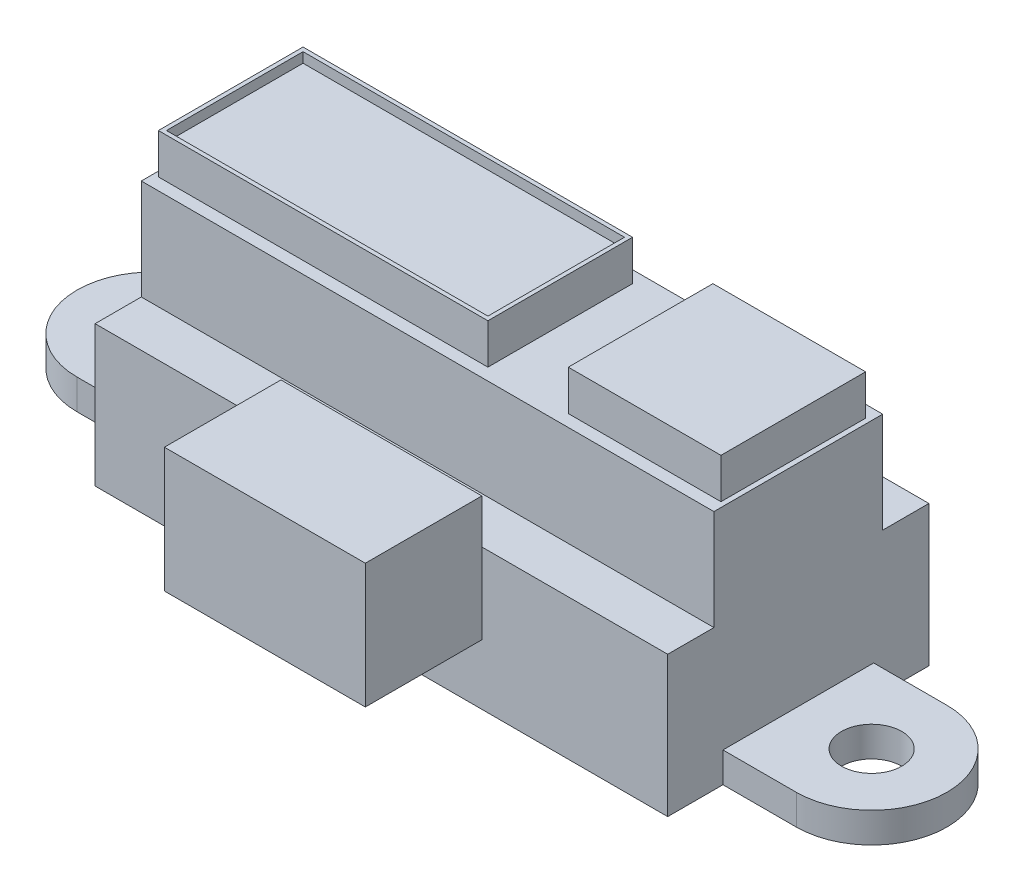
SolidWorks part; units mm, degrees
ref_plane "Front" through (0, 0, 0) normal (0, 0, 1) x (1, 0, 0)
ref_plane "Top" through (0, 0, 0) normal (0, 1, 0) x (1, 0, 0)
ref_plane "Right" through (0, 0, 0) normal (1, 0, 0) x (0, 0, -1)
sketch "Sketch1" plane through (0, 0, 0) normal (0, 1, 0) x (1, 0, 0)
  line L1 (-14.25, -6.5) -> (14.25, -6.5)
  line L2 (-14.25, -6.5) -> (-14.25, 6.5)
  line L3 (-14.25, 6.5) -> (14.25, 6.5)
  line L4 (14.25, -6.5) -> (14.25, 6.5)
  line L5 (-14.25, -6.5) -> (14.25, 6.5) construction
  line L6 (-14.25, 6.5) -> (14.25, -6.5) construction
  point P0 (0, 0)
  dimension "D1" = 28.5
  dimension "D2" = 13
extrude "Boss-Extrude1" add sketch "Sketch1" along normal blind 7
sketch "Sketch2" plane through (0, 7, 0) normal (0, 1, 0) x (1, 0, 0)
  line L0 (14.25, -6.5) -> (14.25, 6.5) construction
  line L1 (-14.25, -4.2) -> (14.25, -4.2)
  line L2 (-14.25, -4.2) -> (-14.25, 4.2)
  line L3 (-14.25, 4.2) -> (14.25, 4.2)
  line L4 (14.25, -4.2) -> (14.25, 4.2)
  line L5 (-14.25, -4.2) -> (14.25, 4.2) construction
  line L6 (-14.25, 4.2) -> (14.25, -4.2) construction
  point P0 (0, 0)
  dimension "D1" = 8.4
extrude "Boss-Extrude2" add sketch "Sketch2" along normal blind 5
sketch "Sketch3" plane through (0, 12, 0) normal (0, 1, 0) x (1, 0, 0)
  line L1 (-14, -3.6) -> (14, -3.6) construction
  line L2 (-14, -3.6) -> (-14, 3.6) construction
  line L3 (-14, 3.6) -> (14, 3.6) construction
  line L4 (14, -3.6) -> (14, 3.6) construction
  line L5 (-14, -3.6) -> (14, 3.6) construction
  line L6 (-14, 3.6) -> (14, -3.6) construction
  point P0 (0, 0)
  point P6 (0, 0)
  point P7 (0, 0)
  dimension "D1" = 28
  dimension "D2" = 7.2
sketch "Sketch4" plane through (0, 12, 0) normal (0, 1, 0) x (1, 0, 0)
  line L1 (-14, 3.6) -> (2.4, 3.6)
  line L2 (-14, 3.6) -> (-14, -3.6)
  line L3 (-14, -3.6) -> (2.4, -3.6)
  line L4 (2.4, 3.6) -> (2.4, -3.6)
  line L5 (14, 3.6) -> (6.4, 3.6)
  line L6 (14, 3.6) -> (14, -3.6)
  line L7 (14, -3.6) -> (6.4, -3.6)
  line L8 (6.4, 3.6) -> (6.4, -3.6)
  point P5 (6.4, -1.4365)
  point P14 (0, 0)
  dimension "D1" = 16.4
  dimension "D2" = 7.6
extrude "Boss-Extrude3" add sketch "Sketch4" along normal blind 2
sketch "Sketch5" plane through (0, 14, 0) normal (0, 1, 0) x (1, 0, 0)
  line L9 (-13.8, 3.4) -> (-13.8, -3.4)
  line L10 (-13.8, -3.4) -> (2.2, -3.4)
  line L11 (2.2, -3.4) -> (2.2, 3.4)
  line L12 (2.2, 3.4) -> (-13.8, 3.4)
  line L13 (-13.8, 3.4) -> (-13.8, -3.4)
  line L14 (-13.8, -3.4) -> (2.2, -3.4)
  line L15 (2.2, -3.4) -> (2.2, 3.4)
  line L16 (2.2, 3.4) -> (-13.8, 3.4)
  dimension "D1" = 0.2
extrude "Cut-Extrude1" cut sketch "Sketch5" against normal blind 0.5
sketch "Sketch6" plane through (0, 0, 0) normal (0, 1, 0) x (1, 0, 0)
  line L0 (-14.25, 6.5) -> (-14.25, -6.5) construction
  line L1 (-14.25, 6.5) -> (-14.25, -6.5) construction
  line L2 (14.25, 0) -> (-14.25, 0) construction
  line L6 (-14.25, 3.75) -> (-14.25, -3.75)
  line L7 (-17.9, 3.75) -> (-17.9, 0) construction
  line L8 (-17.9, 0) -> (-17.9, -3.75) construction
  line L9 (-14.25, -3.75) -> (-17.9, -3.75)
  line L10 (-14.25, 3.75) -> (-17.9, 3.75)
  arc A0 (-17.9, 3.75) -> (-17.9, -3.75) centre (-17.9, 0) ccw
  circle A1 centre (-17.9, 0) radius 1.5
  point P9 (0, 0)
  point P14 (-21.65, 0)
  point P18 (-21.65, 0)
  dimension "D1" = 3.75
  dimension "D3" = 3
  dimension "D2" = 7.4
extrude "Boss-Extrude4" add sketch "Sketch6" along normal blind 1.5
mirror "Mirror1" about plane through (0, 0, 0) normal (1, 0, 0) of "Boss-Extrude4"
ref_plane "Plane1" through (0, 3, 0) normal (0, 1, 0) x (1, 0, 0)
sketch "Sketch7" plane through (0, 3, 0) normal (0, 1, 0) x (1, 0, 0)
  line L0 (0, 0) -> (0, -6.5) construction
  line L1 (-5, -12.3) -> (5, -12.3)
  line L2 (-5, -12.3) -> (-5, -6.5)
  line L3 (-5, -6.5) -> (5, -6.5)
  line L4 (5, -12.3) -> (5, -6.5)
  line L5 (-14.25, -6.5) -> (14.25, -6.5) construction
  point P9 (0, -6.5)
  dimension "D1" = 10
  dimension "D2" = 5.8
extrude "Boss-Extrude5" add sketch "Sketch7" along normal blind 6.2
